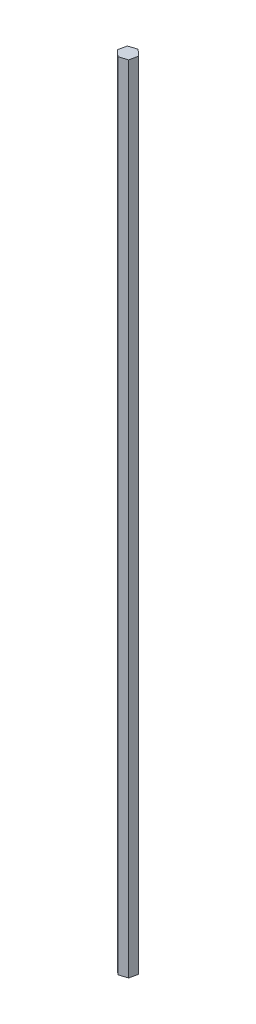
SolidWorks part; units mm, degrees
ref_plane "Front Plane" through (0, 0, 0) normal (0, 0, 1) x (1, 0, 0)
ref_plane "Top Plane" through (0, 0, 0) normal (0, 1, 0) x (1, 0, 0)
ref_plane "Right Plane" through (0, 0, 0) normal (1, 0, 0) x (0, 0, -1)
sketch "Sketch1" plane through (0, 0, 0) normal (0, 1, 0) x (1, 0, 0)
  line L7 (2.0836, -0.3657) -> (3.6227, 6.8033)
  line L8 (3.6227, 6.8033) -> (-1.8163, 11.7207)
  line L9 (-1.8163, 11.7207) -> (-8.7944, 9.4691)
  line L10 (-8.7944, 9.4691) -> (-10.3335, 2.3001)
  line L11 (-10.3335, 2.3001) -> (-4.8945, -2.6173)
  line L12 (-4.8945, -2.6173) -> (2.0836, -0.3657)
  circle A0 centre (-3.3554, 4.5517) radius 6.35 construction
  dimension "D1" = 12.7
extrude "Boss-Extrude1" add sketch "Sketch1" along normal blind 685.8
